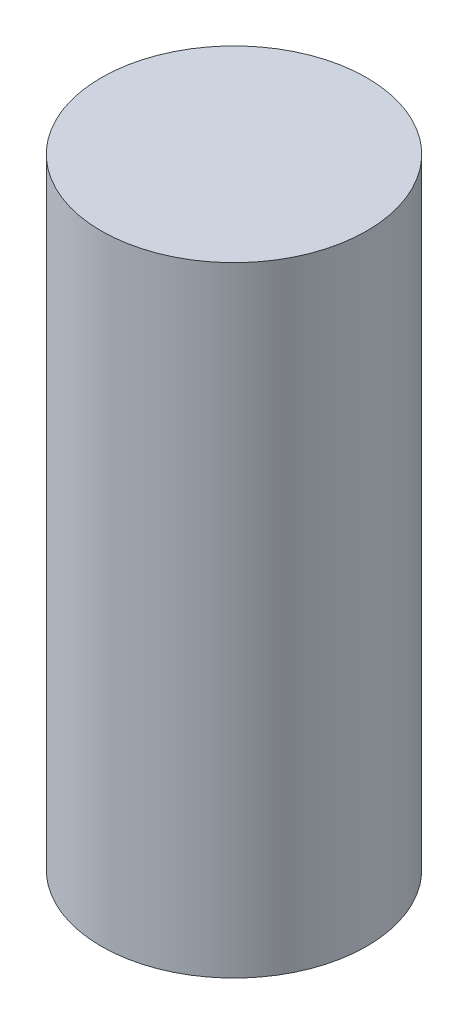
SolidWorks part; units mm, degrees
ref_plane "Front Plane" through (0, 0, 0) normal (0, 0, 1) x (1, 0, 0)
ref_plane "Top Plane" through (0, 0, 0) normal (0, 1, 0) x (1, 0, 0)
ref_plane "Right Plane" through (0, 0, 0) normal (1, 0, 0) x (0, 0, -1)
sketch "Sketch1" plane through (0, 0, 0) normal (0, 1, 0) x (1, 0, 0)
  circle A0 centre (0, 0) radius 19.05
  dimension "D1" = 38.1
extrude "Boss-Extrude1" add sketch "Sketch1" along normal blind 88.9
